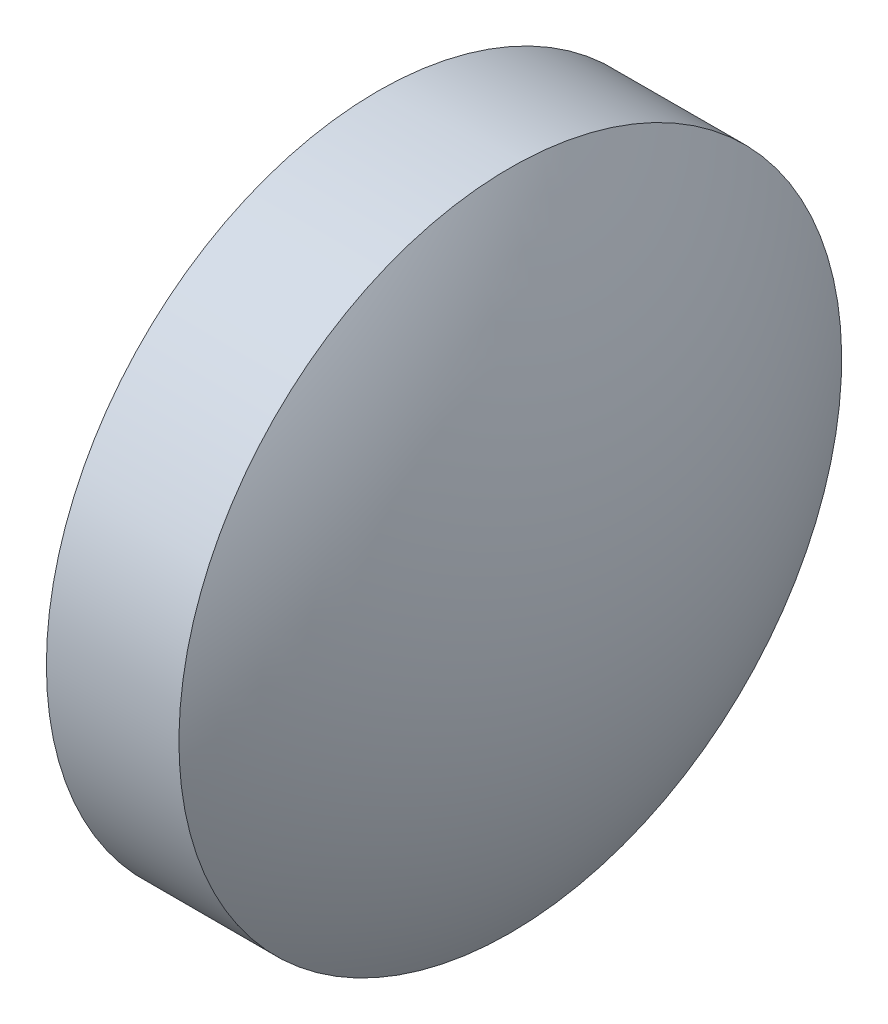
SolidWorks part; units mm, degrees
ref_plane "前视基准面" through (0, 0, 0) normal (0, 0, 1) x (1, 0, 0)
ref_plane "上视基准面" through (0, 0, 0) normal (0, 1, 0) x (1, 0, 0)
ref_plane "右视基准面" through (0, 0, 0) normal (1, 0, 0) x (0, 0, -1)
sketch "草图2" plane through (0, 0, 0) normal (0, 0, 1) x (1, 0, 0)
  line L0 (33.0387, 24.1402) -> (35.0387, 24.1402)
  line L1 (35.0387, 24.1402) -> (35.0387, 14.1402)
  line L2 (35.0387, 14.1402) -> (33.0387, 14.1402)
  line L3 (33.0387, 14.1402) -> (33.0387, 24.1402)
  line L4 (27.0454, 19.1402) -> (41.032, 19.1402) construction
  arc A0 (33.0387, 24.1402) -> (33.0387, 14.1402) centre (41.032, 19.1402) ccw
  arc A1 (35.0387, 14.1402) -> (35.0387, 24.1402) centre (27.0454, 19.1402) ccw
  dimension "D1" = 2
  dimension "D2" = 10
revolve "旋转1" add sketch "草图2" angle 360 about L4
